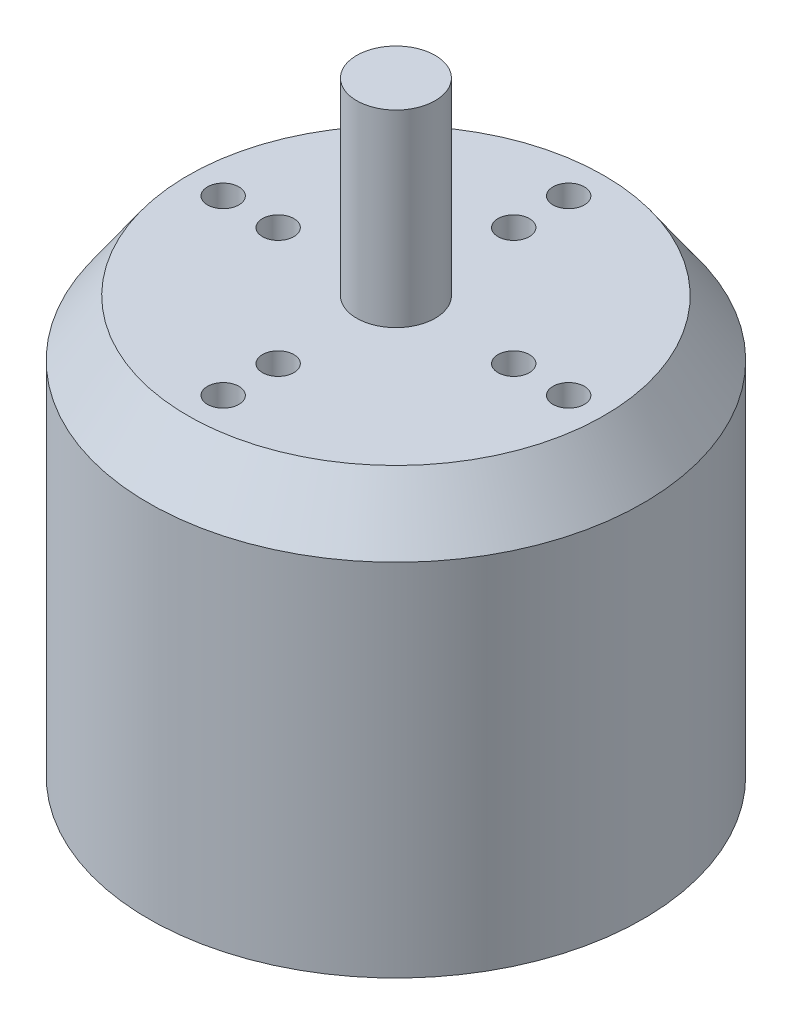
SolidWorks part; units mm, degrees
ref_plane "Front Plane" through (0, 0, 0) normal (0, 0, 1) x (1, 0, 0)
ref_plane "Top Plane" through (0, 0, 0) normal (0, 1, 0) x (1, 0, 0)
ref_plane "Right Plane" through (0, 0, 0) normal (1, 0, 0) x (0, 0, -1)
sketch "Sketch1" plane through (0, 0, 0) normal (0, 0, 1) x (1, 0, 0)
  line L1 (0, 0) -> (31.5, 0)
  line L2 (0, 0) -> (0, 55)
  line L3 (0, 55) -> (31.5, 55)
  line L4 (31.5, 0) -> (31.5, 55)
  line L5 (0, 55) -> (5, 55)
  line L6 (0, 55) -> (0, 79)
  line L7 (0, 79) -> (5, 79)
  line L8 (5, 55) -> (5, 79)
  dimension "D1" = 31.5
  dimension "D2" = 55
  dimension "D3" = 5
  dimension "D4" = 24
revolve "Revolve1" add sketch "Sketch1" angle 360 about L6
chamfer "Chamfer1" distance 5 angle 55 1 edges at (0, 55, -31.5)
chamfer "Chamfer2" distance 2 angle 55 1 edges at (0, 0, -31.5)
hole_wizard "Ø4.0mm Dowel Hole1" positions "Sketch2" profile "Sketch3" hole size "Ø4.0" standard "ANSI Metric"
sketch "Sketch2" plane through (0, 55, 0) normal (0, 1, 0) x (1, 0, 0)
  circle A1 centre (0, 0) radius 22
  circle A2 centre (0, 0) radius 15
  point P7 (0, 22)
  point P9 (22, 0)
  point P11 (0, -22)
  point P13 (-22, 0)
  point P19 (0, 15)
  point P20 (-15, 0)
  point P22 (0, -15)
  point P24 (15, 0)
  dimension "D1" = 44
  dimension "D2" = 30
sketch "Sketch3" plane through (15, 55, 0) normal (1, 0, 0) x (0, 0, 1)
  line L0 (0, 0) -> (0, 21.2017)
  line L1 (0, 21.2017) -> (2, 20)
  line L2 (2, 20) -> (2, 0)
  line L5 (2, 0) -> (0, 0)
  line L10 (0, 21.2017) -> (-2, 20) construction
  line L11 (0, -6.35) -> (0, 107.95) construction
  dimension "Hole Dia." = 4
  dimension "Hole Depth" = 20
  dimension "Drill Angle" = 118
